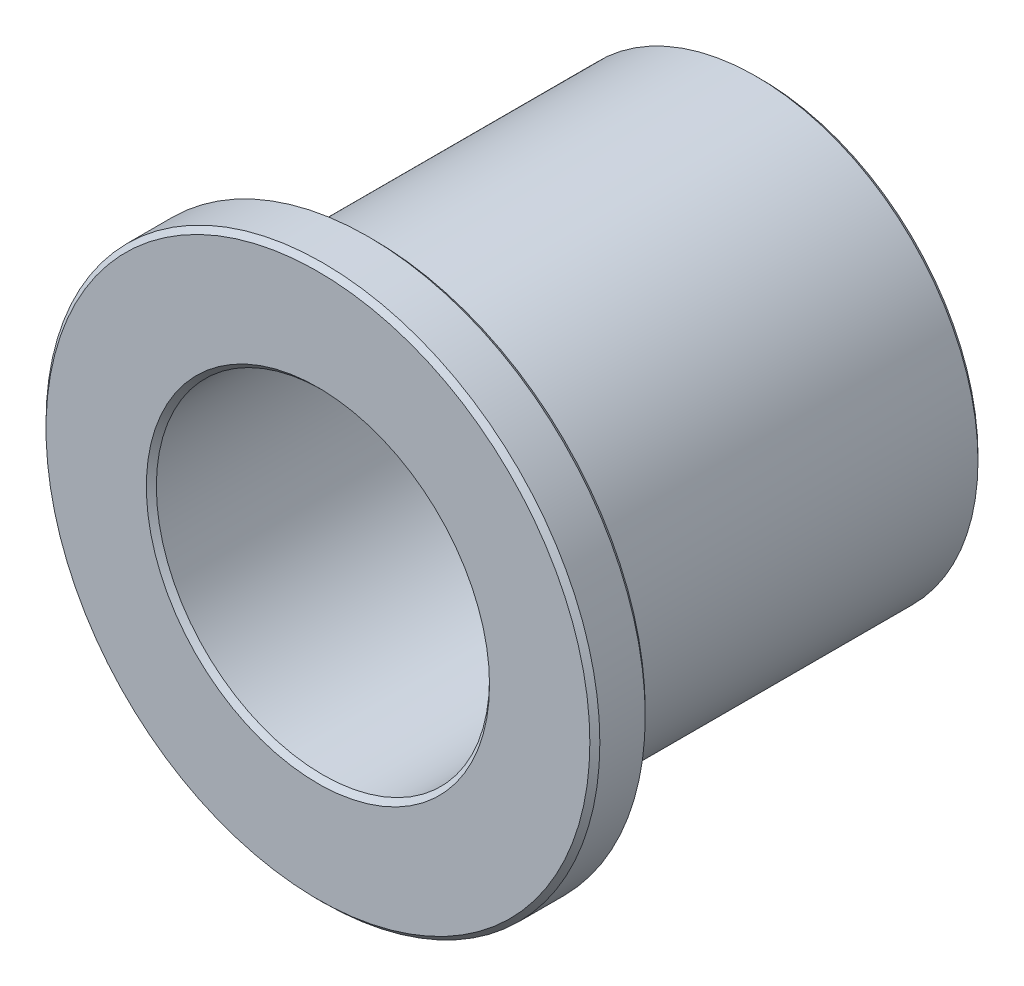
SolidWorks part; units mm, degrees
material "AISI Type A2 Tool Steel"
ref_plane "Front" through (0, 0, 0) normal (0, 0, 1) x (1, 0, 0)
ref_plane "Top" through (0, 0, 0) normal (0, 1, 0) x (1, 0, 0)
ref_plane "Right" through (0, 0, 0) normal (1, 0, 0) x (0, 0, -1)
sketch "Sketch1" plane through (0, 0, 0) normal (0, 0, 1) x (1, 0, 0)
  circle A0 centre (0, 0) radius 4.7752
  circle A1 centre (0, 0) radius 6.3627
  circle A2 centre (0, 0) radius 7.9375
  dimension "ID" = 9.5504
  dimension "OD" = 12.7254
  dimension "Flange OD" = 15.875
sketch "Sketch2" plane through (0, 0, 0) normal (1, 0, 0) x (0, 0, -1)
  line L0 (-6.35, -7.9375) -> (6.35, -7.9375) construction
  line L1 (0, 7.9375) -> (0, -7.9375) construction
  line L3 (-4.7625, 6.3627) -> (6.35, 6.3627) construction
  point P3 (0, -7.9375)
  point P7 (0, 6.3627)
  point P9 (-4.7625, -7.9375)
  point P10 (-6.35, 7.9375)
  point P23 (0, 7.9375)
  dimension "Flange Thickness" = 1.5875
  dimension "Length" = 12.7
sketch "Sketch3" plane through (0, 0, 0) normal (0, 0, 1) x (1, 0, 0)
  circle A0 centre (0, 0) radius 7.9375 construction
  circle A1 centre (0, 0) radius 7.9375
  circle A2 centre (0, 0) radius 4.7752 construction
  circle A3 centre (0, 0) radius 4.7752
extrude "Boss-Extrude1" add sketch "Sketch3" against normal up to vertex (-4.7625 mm away) from vertex at 6.35 starting at point (0, -7.9375, 6.35)
sketch "Sketch4" plane through (0, 0, 0) normal (0, 0, 1) x (1, 0, 0)
  circle A0 centre (0, 0) radius 4.7752 construction
  circle A1 centre (0, 0) radius 6.3627 construction
  circle A2 centre (0, 0) radius 4.7752
  circle A3 centre (0, 0) radius 6.3627
extrude "Boss-Extrude2" add sketch "Sketch4" against normal up to vertex (6.35 mm away) from vertex at 4.7625 starting at point (0, -7.9375, 4.7625)
chamfer "Chamfer1" distance 0.1433 angle 45 6 edges at (4.7752, 0, 6.35) (7.9375, 0, 6.35) (7.9375, 0, 4.7625) (6.3627, 0, 4.7625) (4.7752, 0, -6.35) (6.3627, 0, -6.35)
equation "\"D1@Chamfer1\"=\"ID@Sketch1\"*0.015"
